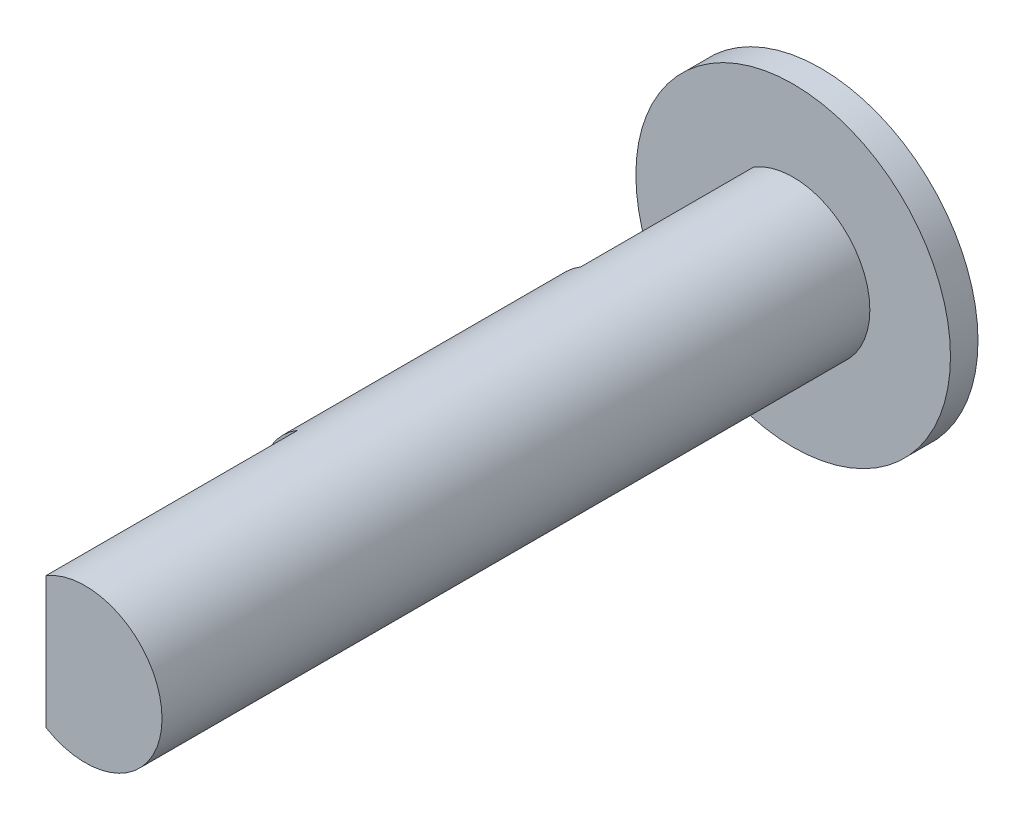
SolidWorks part; units mm, degrees
ref_plane "Front Plane" through (0, 0, 0) normal (0, 0, 1) x (1, 0, 0)
ref_plane "Top Plane" through (0, 0, 0) normal (0, 1, 0) x (1, 0, 0)
ref_plane "Right Plane" through (0, 0, 0) normal (1, 0, 0) x (0, 0, -1)
sketch "Sketch2" plane through (0, 0, 0) normal (0, 0, 1) x (1, 0, 0)
  circle A0 centre (0, 0) radius 1.95
  dimension "D1" = 3.9
extrude "Boss-Extrude1" add sketch "Sketch2" along normal mid plane 18
sketch "Sketch4" plane through (0, 0, -9) normal (0, 0, -1) x (-1, 0, 0)
  line L0 (1, 1.6741) -> (1, -1.6741)
  arc A0 (1, -1.6741) -> (1, 1.6741) centre (0, 0) ccw
  dimension "D2" = 3.9
  dimension "D1" = 1
extrude "Cut-Extrude1" cut sketch "Sketch4" against normal blind 4.4
ref_plane "Plane1" through (0, 0, -9) normal (0, 0, -1) x (-1, 0, 0)
sketch "Sketch5" plane through (0, 0, -9) normal (0, 0, -1) x (-1, 0, 0)
  circle A0 centre (0, 0) radius 4
  dimension "D1" = 8
extrude "Boss-Extrude2" add sketch "Sketch5" along normal blind 0.7
ref_plane "Plane2" through (0, 0, 9) normal (0, 0, 1) x (1, 0, 0)
sketch "Sketch9" plane through (0, 0, 9) normal (0, 0, 1) x (1, 0, 0)
  line L0 (-1, 1.6741) -> (-1, -1.6741)
  arc A0 (-1, 1.6741) -> (-1, -1.6741) centre (0, 0) ccw
  dimension "D2" = 3.9
  dimension "D1" = 1
extrude "Cut-Extrude2" cut sketch "Sketch9" against normal blind 6.4
